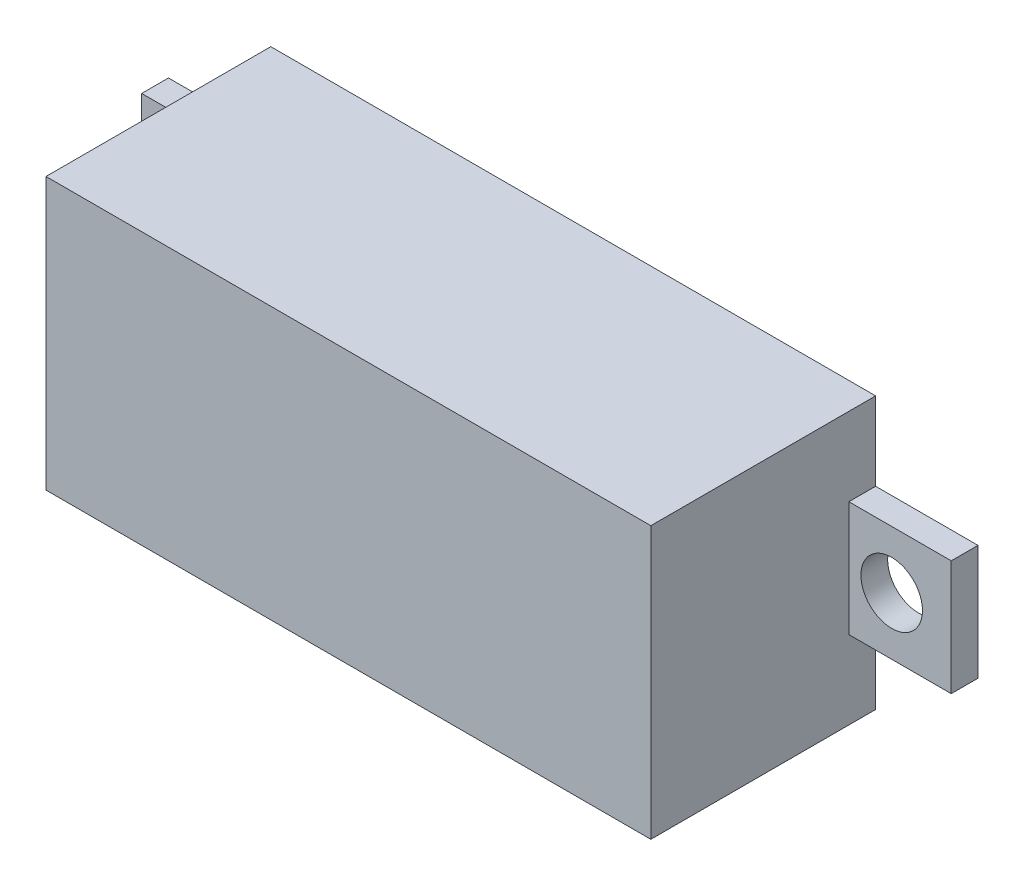
SolidWorks part; units mm, degrees
ref_plane "Front Plane" through (0, 0, 0) normal (0, 0, 1) x (1, 0, 0)
ref_plane "Top Plane" through (0, 0, 0) normal (0, 1, 0) x (1, 0, 0)
ref_plane "Right Plane" through (0, 0, 0) normal (1, 0, 0) x (0, 0, -1)
sketch "Sketch1" plane through (0, 0, 0) normal (0, 0, 1) x (1, 0, 0)
  line L1 (-11.3, 5.075) -> (11.3, 5.075)
  line L2 (-11.3, 5.075) -> (-11.3, -5.075)
  line L3 (-11.3, -5.075) -> (11.3, -5.075)
  line L4 (11.3, 5.075) -> (11.3, -5.075)
  point P4 (0, 5.075)
  point P5 (11.3, 0)
  point P6 (0, 0)
  point P8 (0, 0)
  point P9 (0, 0)
  dimension "D1" = 22.6
  dimension "D2" = 10.15
extrude "Main" add sketch "Sketch1" along normal blind 8.4
sketch "Sketch2" plane through (0, 0, 0) normal (0, 0, 1) x (1, 0, 0)
  line L0 (-11.3, 5.075) -> (-11.3, -5.075) construction
  line L1 (-11.3, 2.15) -> (-15.125, 2.15)
  line L2 (-11.3, 2.15) -> (-11.3, -2.15)
  line L3 (-11.3, -2.15) -> (-15.125, -2.15)
  line L4 (-15.125, 2.15) -> (-15.125, -2.15)
  line L5 (11.3, -5.075) -> (11.3, 5.075) construction
  line L6 (11.3, 2.15) -> (15.125, 2.15)
  line L7 (11.3, 2.15) -> (11.3, -2.15)
  line L8 (11.3, -2.15) -> (15.125, -2.15)
  line L9 (15.125, 2.15) -> (15.125, -2.15)
  circle A0 centre (-12.9, 0) radius 1.15
  circle A1 centre (12.9, 0) radius 1.15
  point P12 (-15.125, 0)
  point P18 (0, 0)
  dimension "D3" = 2.3
  dimension "D1" = 4.3
  dimension "D2" = 30.25
  dimension "D4" = 1.6
  dimension "D5" = 1.6
  dimension "D6" = 25.8
  dimension "D7" = 22.6
extrude "Fix" add sketch "Sketch2" along normal blind 1 separate body
